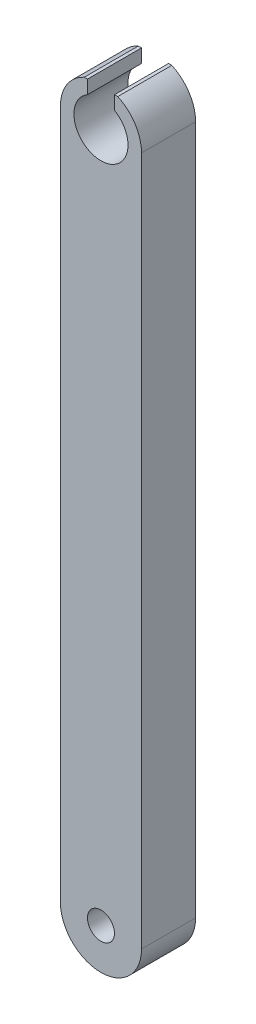
SolidWorks part; units mm, degrees
ref_plane "前视基准面" through (0, 0, 0) normal (0, 0, 1) x (1, 0, 0)
ref_plane "上视基准面" through (0, 0, 0) normal (0, 1, 0) x (1, 0, 0)
ref_plane "右视基准面" through (0, 0, 0) normal (1, 0, 0) x (0, 0, -1)
other "Configuration Table"
sketch "草图1" plane through (0, 0, 0) normal (0, 0, 1) x (1, 0, 0)
  line L0 (0, -1000) -> (0, 49000) construction
  line L1 (-1.5, 0) -> (-1.5, 30)
  line L2 (1.5, 0) -> (1.5, 30)
  circle A0 centre (0, 0) radius 1.5
  circle A1 centre (0, 25.5) radius 1.5
  circle A2 centre (0, 0) radius 0.5
  dimension "D1" = 3
  dimension "D2" = 3
  dimension "D4" = 1
  dimension "D3" = 25.5
extrude "凸台-拉伸1" add sketch "草图1" along normal blind 2 contours L0 A0 L2 A1 | L0 A1 | A1 L0 | A0 L0 A1 L1 | L0 A0 A2 | A0 L0 A2
sketch "草图2" plane through (0, 0, 2) normal (0, 0, 1) x (1, 0, 0)
  line L0 (0, -970) -> (0, 49030) construction
  line L1 (-0.5, 26.366) -> (-0.5, 26.9142)
  line L2 (0.5, 26.366) -> (0.5, 26.9142)
  line L3 (-0.5, 26.866) -> (0.5, 26.866)
  line L4 (-0.5, 26.866) -> (-0.6197, 26.866)
  line L5 (0.5, 26.866) -> (0.6197, 26.866)
  circle A0 centre (0, 25.5) radius 1
  arc A1 (1.5, 25.5) -> (-1.5, 25.5) centre (0, 25.5) ccw construction
  arc A2 (1.5, 25.5) -> (-1.5, 25.5) centre (0, 25.5) ccw
  arc M9 (1.5, 25.5) -> (-1.5, 25.5) centre (0, 25.5) ccw
  dimension "D1" = 2
  dimension "D2" = 1
  dimension "D3" = 0.5
extrude "切除-拉伸1" cut sketch "草图2" against normal blind 10 contours A0 L0 | L0 A0 | L0 A0 L2 L3 | A0 L0 L3 L1 | L4 L1 M9 | L3 L0 A2 L1 | L0 L3 L2 M9 | L2 L5 M9
